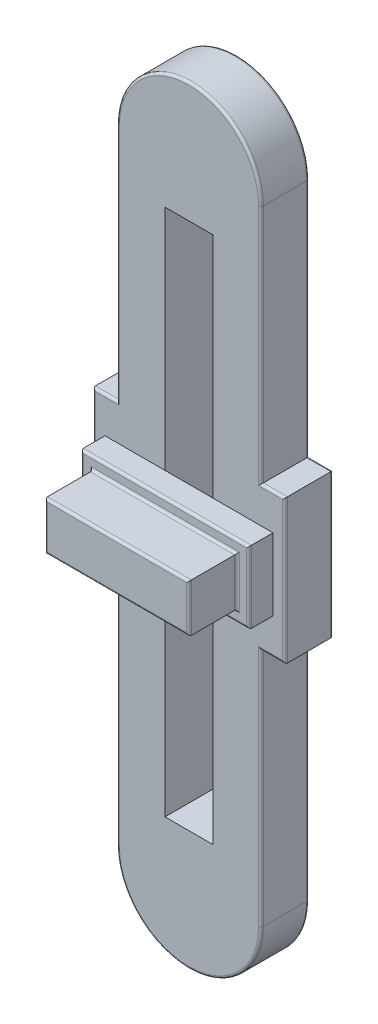
SolidWorks part; units mm, degrees
ref_plane "Front Plane" through (0, 0, 0) normal (0, 0, 1) x (1, 0, 0)
ref_plane "Top Plane" through (0, 0, 0) normal (0, 1, 0) x (1, 0, 0)
ref_plane "Right Plane" through (0, 0, 0) normal (1, 0, 0) x (0, 0, -1)
sketch "Sketch1" plane through (0, 0, 0) normal (0, 0, 1) x (1, 0, 0)
  line L0 (0, 0) -> (0, -260) construction
  line L1 (30, 0) -> (30, -100)
  line L2 (-30, 0) -> (-30, -100)
  line L3 (-30, -130) -> (73.4166, -130) construction
  line L4 (-10, -20) -> (10, -20)
  line L5 (-10, -20) -> (-10, -240)
  line L6 (-10, -240) -> (10, -240)
  line L7 (10, -20) -> (10, -240)
  line L8 (-10, -20) -> (10, -240) construction
  line L9 (-10, -240) -> (10, -20) construction
  line L10 (-30, -160) -> (-30, -260)
  line L11 (-30, -100) -> (-40, -100)
  line L13 (-30, -160) -> (-40, -160)
  line L14 (-40, -100) -> (-40, -160)
  line L15 (-30, -100) -> (-40, -160) construction
  line L16 (-30, -160) -> (-40, -100) construction
  line L17 (30, -100) -> (40, -100)
  line L19 (30, -160) -> (40, -160)
  line L20 (40, -100) -> (40, -160)
  line L21 (30, -100) -> (40, -160) construction
  line L22 (30, -160) -> (40, -100) construction
  line L23 (30, -160) -> (30, -260)
  arc A0 (30, 0) -> (-30, 0) centre (0, 0) ccw
  arc A1 (-30, -260) -> (30, -260) centre (0, -260) ccw
  point P3 (0, -130)
  point P12 (0, -130)
  point P19 (-35, -130)
  point P24 (35, -130)
  dimension "D2" = 30
  dimension "D1" = 260
  dimension "D3" = 20
  dimension "D4" = 220
  dimension "D5" = 10
  dimension "D6" = 60
  dimension "D7" = 20
extrude "Boss-Extrude1" add sketch "Sketch1" along normal blind 20
sketch "Sketch2" plane through (0, 0, 20) normal (0, 0, 1) x (1, 0, 0)
  line L0 (-40, -130) -> (40, -130) construction
  line L1 (-40, -100) -> (-40, -160) construction
  line L2 (40, -160) -> (40, -100) construction
  line L4 (30, -140) -> (-30, -140)
  line L5 (30, -140) -> (30, -120)
  line L6 (30, -120) -> (-30, -120)
  line L7 (-30, -140) -> (-30, -120)
  line L8 (30, -140) -> (-30, -120) construction
  line L9 (30, -120) -> (-30, -140) construction
  point P6 (0, -130)
  dimension "D1" = 60
  dimension "D2" = 20
extrude "Boss-Extrude2" add sketch "Sketch2" along normal blind 30
sketch "Sketch3" plane through (0, 0, 20) normal (0, 0, 1) x (1, 0, 0)
  line L1 (35, -115) -> (-35, -115)
  line L2 (-35, -115) -> (-35, -145)
  line L3 (-35, -145) -> (35, -145)
  line L4 (-30, -120) -> (-30, -140)
  line L5 (-30, -140) -> (30, -140)
  line L6 (30, -140) -> (30, -120)
  line L7 (30, -120) -> (-30, -120)
  line L8 (-30, -120) -> (-30, -140)
  line L9 (-30, -140) -> (30, -140)
  line L10 (30, -140) -> (30, -120)
  line L11 (30, -120) -> (-30, -120)
  line L12 (35, -145) -> (35, -115)
  dimension "D1" = 0
  dimension "D2" = 5
extrude "Boss-Extrude3" add sketch "Sketch3" along normal blind 10
fillet "Fillet1" radius 1 12 edges at (0, -120, 50) (30, -130, 50) (0, -140, 50) (-30, -130, 50) (0, -140, 30) (30, -130, 30) (0, -120, 30) (-30, -130, 30) (0, -145, 30) (-35, -130, 30) (0, -115, 30) (35, -130, 30)
fillet "Fillet2" radius 1 24 edges at (-30, -210, 0) (30, -210, 0) (30, -50, 0) (-30, -50, 0) (30, -50, 20) (-30, -50, 20) (-30, -210, 20) (30, -210, 20) (-35, -100, 20) (-35, -160, 20) (-40, -130, 20) (35, -160, 20) (35, -100, 20) (40, -130, 20) (35, -160, 0) (-35, -160, 0) (-35, -100, 0) (-40, -130, 0) (40, -130, 0) (35, -100, 0) (0, -290, 0) (0, 30, 0) (0, 30, 20) (0, -290, 20)
